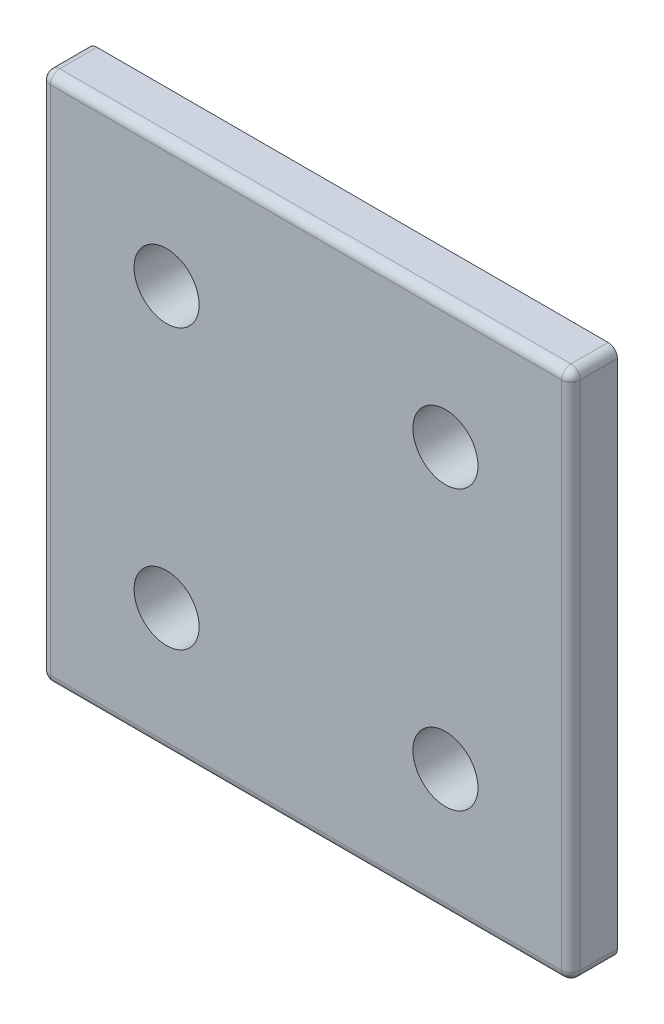
SolidWorks part; units mm, degrees
material "6061-T6 (SS)"
ref_plane "Front Plane" through (0, 0, 0) normal (0, 0, 1) x (1, 0, 0)
ref_plane "Top Plane" through (0, 0, 0) normal (0, 1, 0) x (1, 0, 0)
ref_plane "Right Plane" through (0, 0, 0) normal (1, 0, 0) x (0, 0, -1)
sketch "Sketch1" plane through (0, 0, 0) normal (0, 0, 1) x (1, 0, 0)
  line L0 (0, 0) -> (0, 57)
  line L1 (13.5, 13.5) -> (43.5, 13.5) construction
  line L2 (13.5, 13.5) -> (13.5, 43.5) construction
  line L3 (13.5, 43.5) -> (43.5, 43.5) construction
  line L4 (57, 57) -> (0, 57)
  line L5 (57, 0) -> (0, 0)
  line L6 (43.5, 43.5) -> (43.5, 13.5) construction
  line L7 (57, 57) -> (57, 0)
  circle A0 centre (13.5, 13.5) radius 3.5
  circle A1 centre (43.5, 13.5) radius 3.5
  circle A2 centre (13.5, 43.5) radius 3.5
  circle A3 centre (43.5, 43.5) radius 3.5
  dimension "D1" = 30
  dimension "E" = 7
  dimension "D2" = 13.5
  dimension "C" = 57
  dimension "D3" = 30
  dimension "B" = 57
  dimension "D4" = 13.5
extrude "Boss-Extrude1" add sketch "Sketch1" along normal mid plane 5
fillet "Fillet1" radius 1 8 edges at (0, 0, 0) (0, 28.5, 2.5) (28.5, 0, 2.5) (57, 28.5, 2.5) (57, 0, 0) (57, 57, 0) (28.5, 57, 2.5) (0, 57, 0)
